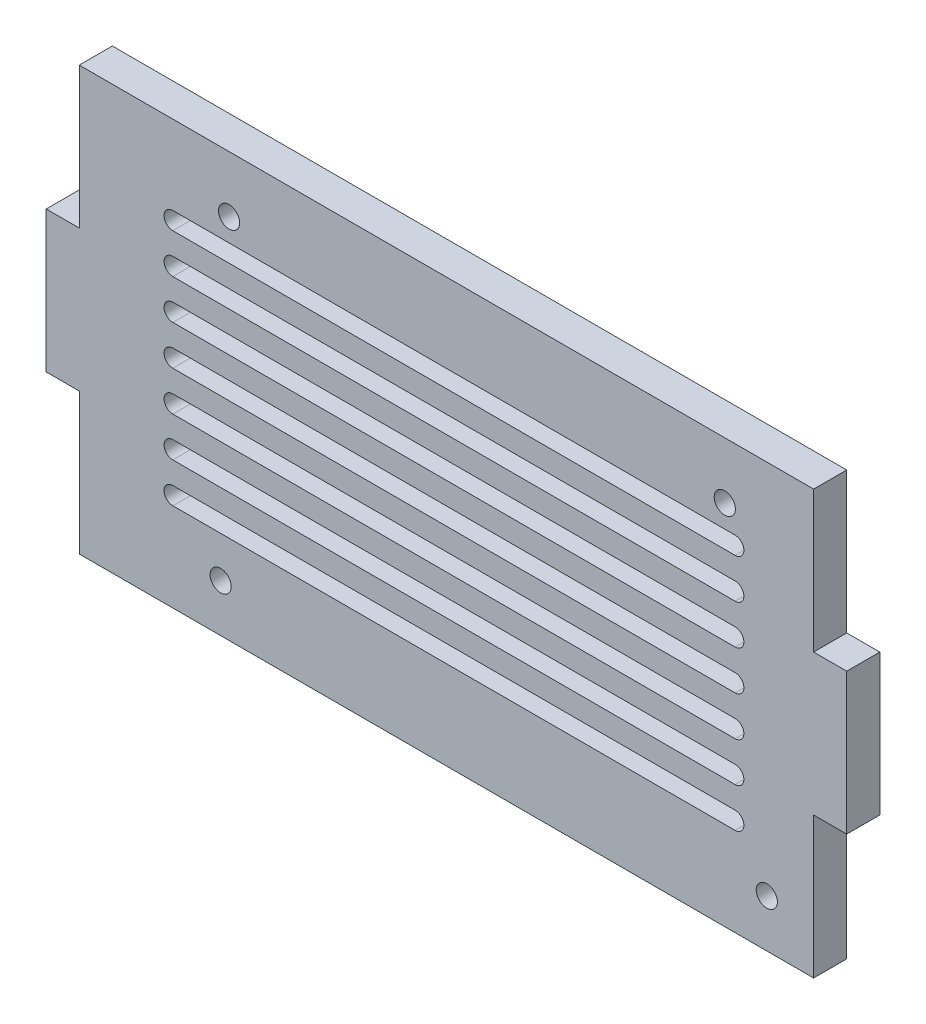
SolidWorks part; units mm, degrees
ref_plane "Alzado" through (0, 0, 0) normal (0, 0, 1) x (1, 0, 0)
ref_plane "Planta" through (0, 0, 0) normal (0, 1, 0) x (1, 0, 0)
ref_plane "Vista lateral" through (0, 0, 0) normal (1, 0, 0) x (0, 0, -1)
sketch "Croquis1" plane through (0, 0, 0) normal (0, 0, 1) x (1, 0, 0)
  line L0 (63.2484, 20.3599) -> (-33.2876, 20.3599)
  line L1 (-34.2876, 19.3599) -> (-34.2876, -31.9801)
  line L2 (-33.2876, -32.9801) -> (63.7724, -32.9801)
  line L3 (64.7724, -31.9801) -> (64.7724, -30.4401)
  line L4 (64.7724, -30.4401) -> (67.3124, -27.9001)
  line L5 (67.3124, -27.9001) -> (67.3124, 4.8659)
  line L6 (67.3124, 4.8659) -> (64.7724, 7.4059)
  line L7 (64.7724, 7.4059) -> (64.7724, 18.8359)
  line L8 (64.7724, 18.8359) -> (63.2484, 20.3599)
  line L9 (-27.5479, 13.0737) -> (57.4412, 13.0737) construction
  line L10 (-41.6876, 26.3599) -> (69.3124, 26.3599)
  line L11 (-41.6876, 26.3599) -> (-41.6876, -37.6401)
  line L12 (-41.6876, -37.6401) -> (69.3124, -37.6401)
  line L13 (69.3124, 26.3599) -> (69.3124, -37.6401)
  line L14 (-27.5479, 14.3982) -> (57.4412, 14.3982)
  line L15 (-27.5479, 11.7492) -> (57.4412, 11.7492)
  line L16 (-27.5479, 7.0737) -> (57.4412, 7.0737) construction
  line L17 (-27.5479, 8.3982) -> (57.4412, 8.3982)
  line L18 (-27.5479, 5.7492) -> (57.4412, 5.7492)
  line L19 (-27.5479, 1.0737) -> (57.4412, 1.0737) construction
  line L20 (-27.5479, 2.3982) -> (57.4412, 2.3982)
  line L21 (-27.5479, -0.2508) -> (57.4412, -0.2508)
  line L22 (-27.5479, -4.9263) -> (57.4412, -4.9263) construction
  line L23 (-27.5479, -3.6018) -> (57.4412, -3.6018)
  line L24 (-27.5479, -6.2508) -> (57.4412, -6.2508)
  line L25 (-27.5479, -10.9263) -> (57.4412, -10.9263) construction
  line L26 (-27.5479, -9.6018) -> (57.4412, -9.6018)
  line L27 (-27.5479, -12.2508) -> (57.4412, -12.2508)
  line L28 (-27.5479, -16.9263) -> (57.4412, -16.9263) construction
  line L29 (-27.5479, -15.6018) -> (57.4412, -15.6018)
  line L30 (-27.5479, -18.2508) -> (57.4412, -18.2508)
  line L31 (-27.5479, -22.9263) -> (57.4412, -22.9263) construction
  line L32 (-27.5479, -21.6018) -> (57.4412, -21.6018)
  line L33 (-27.5479, -24.2508) -> (57.4412, -24.2508)
  circle A4 centre (-20.3176, -30.4401) radius 1.6
  circle A5 centre (-19.0476, 17.8199) radius 1.6
  circle A6 centre (55.8824, 17.8199) radius 1.6
  circle A7 centre (62.2324, -30.4401) radius 1.6
  arc A8 (-33.2876, 20.3599) -> (-34.2876, 19.3599) centre (-33.2876, 19.3599) ccw
  arc A9 (-34.2876, -31.9801) -> (-33.2876, -32.9801) centre (-33.2876, -31.9801) ccw
  arc A10 (63.7724, -32.9801) -> (64.7724, -31.9801) centre (63.7724, -31.9801) ccw
  arc A39 (-27.5479, 14.3982) -> (-27.5479, 11.7492) centre (-27.5479, 13.0737) ccw
  arc A40 (57.4412, 11.7492) -> (57.4412, 14.3982) centre (57.4412, 13.0737) ccw
  arc A41 (-27.5479, 8.3982) -> (-27.5479, 5.7492) centre (-27.5479, 7.0737) ccw
  arc A42 (57.4412, 5.7492) -> (57.4412, 8.3982) centre (57.4412, 7.0737) ccw
  arc A43 (-27.5479, 2.3982) -> (-27.5479, -0.2508) centre (-27.5479, 1.0737) ccw
  arc A44 (57.4412, -0.2508) -> (57.4412, 2.3982) centre (57.4412, 1.0737) ccw
  arc A45 (-27.5479, -3.6018) -> (-27.5479, -6.2508) centre (-27.5479, -4.9263) ccw
  arc A46 (57.4412, -6.2508) -> (57.4412, -3.6018) centre (57.4412, -4.9263) ccw
  arc A47 (-27.5479, -9.6018) -> (-27.5479, -12.2508) centre (-27.5479, -10.9263) ccw
  arc A48 (57.4412, -12.2508) -> (57.4412, -9.6018) centre (57.4412, -10.9263) ccw
  arc A49 (-27.5479, -15.6018) -> (-27.5479, -18.2508) centre (-27.5479, -16.9263) ccw
  arc A50 (57.4412, -18.2508) -> (57.4412, -15.6018) centre (57.4412, -16.9263) ccw
  arc A51 (-27.5479, -21.6018) -> (-27.5479, -24.2508) centre (-27.5479, -22.9263) ccw
  arc A52 (57.4412, -24.2508) -> (57.4412, -21.6018) centre (57.4412, -22.9263) ccw
  point P30 (14.9467, 13.0737)
  point P38 (14.9467, 7.0737)
  point P45 (14.9467, 1.0737)
  point P52 (14.9467, -4.9263)
  point P59 (14.9467, -10.9263)
  point P66 (14.9467, -16.9263)
  point P73 (14.9467, -22.9263)
  dimension "D1" = 3.2
  dimension "D2" = 1
  dimension "D3" = 55.8824
  dimension "D4" = 62.2324
  dimension "D5" = 63.2484
  dimension "D6" = 64.7724
  dimension "D7" = 67.3124
  dimension "D8" = 19.0476
  dimension "D9" = 20.3176
  dimension "D10" = 34.2876
  dimension "D11" = 4.8659
  dimension "D12" = 7.4059
  dimension "D13" = 17.8199
  dimension "D14" = 18.8359
  dimension "D15" = 20.3599
  dimension "D16" = 27.9001
  dimension "D17" = 111
  dimension "D18" = 32.9801
  dimension "D19" = 64
  dimension "D20" = 6
  dimension "D21" = 7
  dimension "D23" = 2
extrude "Saliente-Extruir1" add sketch "Croquis1" along normal blind 5 contours L13 L10 L11 L12 A10 L2 A9 L1 A8 L0 L8 L7 L6 L5 L4 L3 | L2 A10 L3 L4 L5 L6 L7 L8 L0 A8 L1 A9 A4 A5 A6 A7
sketch "Croquis2" plane through (-41.6876, 0, 0) normal (-1, 0, 0) x (0, 0, 1)
  line L0 (0, 26.3599) -> (0, -37.6401) construction
  line L1 (0, 5.0266) -> (5, 5.0266)
  line L2 (0, 5.0266) -> (0, -16.3067)
  line L3 (0, -16.3067) -> (5, -16.3067)
  line L4 (5, 5.0266) -> (5, -16.3067)
  line L5 (5, 26.3599) -> (5, -37.6401) construction
  line L6 (5, 26.3599) -> (0, 26.3599) construction
  dimension "D1" = 21.3333
  dimension "D2" = 21.3333
extrude "Saliente-Extruir2" add sketch "Croquis2" along normal blind 5
sketch "Croquis3" plane through (69.3124, 0, 0) normal (1, 0, 0) x (0, 0, -1)
  line L0 (-5, 26.3599) -> (-5, -37.6401) construction
  line L1 (-5, 5.0266) -> (0, 5.0266)
  line L2 (-5, 5.0266) -> (-5, -16.3067)
  line L3 (-5, -16.3067) -> (0, -16.3067)
  line L4 (0, 5.0266) -> (0, -16.3067)
  line L5 (0, 26.3599) -> (0, -37.6401) construction
  line L6 (-5, 26.3599) -> (0, 26.3599) construction
  dimension "D1" = 21.3333
  dimension "D2" = 21.3333
extrude "Saliente-Extruir3" add sketch "Croquis3" along normal blind 5
sketch "Croquis4" plane through (0, 0, 5) normal (0, 0, 1) x (1, 0, 0)
  line L0 (-27.5479, -0.2508) -> (57.4412, -0.2508) construction
  line L1 (-27.5479, 14.3982) -> (57.4412, 14.3982) construction
  line L2 (-27.5479, 11.7492) -> (57.4412, 11.7492) construction
  line L3 (-27.5479, 8.3982) -> (57.4412, 8.3982) construction
  line L4 (-27.5479, 5.7492) -> (57.4412, 5.7492) construction
  line L5 (-27.5479, 2.3982) -> (57.4412, 2.3982) construction
  line L6 (-27.5479, -3.6018) -> (57.4412, -3.6018) construction
  line L7 (-27.5479, -6.2508) -> (57.4412, -6.2508) construction
  line L8 (-27.5479, -9.6018) -> (57.4412, -9.6018) construction
  line L9 (-27.5479, -12.2508) -> (57.4412, -12.2508) construction
  line L10 (-27.5479, -18.2508) -> (57.4412, -18.2508) construction
  line L11 (-27.5479, -15.6018) -> (57.4412, -15.6018) construction
  line L12 (69.3124, 5.0266) -> (69.3124, 26.3599)
  line L13 (69.3124, 26.3599) -> (-41.6876, 26.3599)
  line L14 (-41.6876, 26.3599) -> (-41.6876, 5.0266)
  line L15 (-41.6876, 5.0266) -> (-46.6876, 5.0266)
  line L16 (-46.6876, 5.0266) -> (-46.6876, -16.3067)
  line L17 (-46.6876, -16.3067) -> (-41.6876, -16.3067)
  line L18 (-41.6876, -16.3067) -> (-41.6876, -37.6401)
  line L19 (-41.6876, -37.6401) -> (69.3124, -37.6401)
  line L20 (69.3124, -37.6401) -> (69.3124, -16.3067)
  line L21 (69.3124, -16.3067) -> (74.3124, -16.3067)
  line L22 (74.3124, -16.3067) -> (74.3124, 5.0266)
  line L23 (74.3124, 5.0266) -> (69.3124, 5.0266)
  line L24 (69.3124, 5.0266) -> (69.3124, 26.3599)
  line L25 (69.3124, 26.3599) -> (-41.6876, 26.3599)
  line L26 (-41.6876, 26.3599) -> (-41.6876, 5.0266)
  line L27 (-41.6876, 5.0266) -> (-46.6876, 5.0266)
  line L28 (-46.6876, 5.0266) -> (-46.6876, -16.3067)
  line L29 (-46.6876, -16.3067) -> (-41.6876, -16.3067)
  line L30 (-41.6876, -16.3067) -> (-41.6876, -37.6401)
  line L31 (-41.6876, -37.6401) -> (69.3124, -37.6401)
  line L32 (69.3124, -37.6401) -> (69.3124, -16.3067)
  line L33 (69.3124, -16.3067) -> (74.3124, -16.3067)
  line L34 (74.3124, -16.3067) -> (74.3124, 5.0266)
  line L35 (74.3124, 5.0266) -> (69.3124, 5.0266)
  line L36 (-27.5479, -21.6018) -> (57.4412, -21.6018) construction
  line L37 (-27.5479, -24.2508) -> (57.4412, -24.2508) construction
  line L38 (-27.5479, -0.2508) -> (57.4412, -0.2508)
  line L39 (-27.5479, 14.3982) -> (57.4412, 14.3982)
  line L40 (-27.5479, 11.7492) -> (57.4412, 11.7492)
  line L41 (-27.5479, 8.3982) -> (57.4412, 8.3982)
  line L42 (-27.5479, 5.7492) -> (57.4412, 5.7492)
  line L43 (-27.5479, 2.3982) -> (57.4412, 2.3982)
  line L44 (-27.5479, -3.6018) -> (57.4412, -3.6018)
  line L45 (-27.5479, -6.2508) -> (57.4412, -6.2508)
  line L46 (-27.5479, -9.6018) -> (57.4412, -9.6018)
  line L47 (-27.5479, -12.2508) -> (57.4412, -12.2508)
  line L48 (-27.5479, -18.2508) -> (57.4412, -18.2508)
  line L49 (-27.5479, -15.6018) -> (57.4412, -15.6018)
  line L50 (-27.5479, -21.6018) -> (57.4412, -21.6018)
  line L51 (-27.5479, -24.2508) -> (57.4412, -24.2508)
  arc A0 (57.4412, -24.2508) -> (57.4412, -21.6018) centre (57.4412, -22.9263) ccw construction
  arc A1 (57.4412, -18.2508) -> (57.4412, -15.6018) centre (57.4412, -16.9263) ccw construction
  arc A2 (57.4412, -12.2508) -> (57.4412, -9.6018) centre (57.4412, -10.9263) ccw construction
  arc A3 (57.4412, -6.2508) -> (57.4412, -3.6018) centre (57.4412, -4.9263) ccw construction
  arc A4 (57.4412, -0.2508) -> (57.4412, 2.3982) centre (57.4412, 1.0737) ccw construction
  arc A5 (57.4412, 5.7492) -> (57.4412, 8.3982) centre (57.4412, 7.0737) ccw construction
  arc A6 (57.4412, 11.7492) -> (57.4412, 14.3982) centre (57.4412, 13.0737) ccw construction
  arc A7 (-27.5479, -21.6018) -> (-27.5479, -24.2508) centre (-27.5479, -22.9263) ccw construction
  arc A8 (-27.5479, -15.6018) -> (-27.5479, -18.2508) centre (-27.5479, -16.9263) ccw construction
  arc A9 (-27.5479, -9.6018) -> (-27.5479, -12.2508) centre (-27.5479, -10.9263) ccw construction
  arc A10 (-27.5479, -3.6018) -> (-27.5479, -6.2508) centre (-27.5479, -4.9263) ccw construction
  arc A11 (-27.5479, 2.3982) -> (-27.5479, -0.2508) centre (-27.5479, 1.0737) ccw construction
  arc A12 (-27.5479, 8.3982) -> (-27.5479, 5.7492) centre (-27.5479, 7.0737) ccw construction
  arc A13 (-27.5479, 14.3982) -> (-27.5479, 11.7492) centre (-27.5479, 13.0737) ccw construction
  circle A14 centre (-20.3176, -30.4401) radius 1.6 construction
  circle A15 centre (62.2324, -30.4401) radius 1.6 construction
  circle A16 centre (55.8824, 17.8199) radius 1.6 construction
  circle A17 centre (-19.0476, 17.8199) radius 1.6 construction
  arc A18 (57.4412, -24.2508) -> (57.4412, -21.6018) centre (57.4412, -22.9263) ccw
  arc A19 (57.4412, -18.2508) -> (57.4412, -15.6018) centre (57.4412, -16.9263) ccw
  arc A20 (57.4412, -12.2508) -> (57.4412, -9.6018) centre (57.4412, -10.9263) ccw
  arc A21 (57.4412, -6.2508) -> (57.4412, -3.6018) centre (57.4412, -4.9263) ccw
  arc A22 (57.4412, -0.2508) -> (57.4412, 2.3982) centre (57.4412, 1.0737) ccw
  arc A23 (57.4412, 5.7492) -> (57.4412, 8.3982) centre (57.4412, 7.0737) ccw
  arc A24 (57.4412, 11.7492) -> (57.4412, 14.3982) centre (57.4412, 13.0737) ccw
  arc A25 (-27.5479, -21.6018) -> (-27.5479, -24.2508) centre (-27.5479, -22.9263) ccw
  arc A26 (-27.5479, -15.6018) -> (-27.5479, -18.2508) centre (-27.5479, -16.9263) ccw
  arc A27 (-27.5479, -9.6018) -> (-27.5479, -12.2508) centre (-27.5479, -10.9263) ccw
  arc A28 (-27.5479, -3.6018) -> (-27.5479, -6.2508) centre (-27.5479, -4.9263) ccw
  arc A29 (-27.5479, 2.3982) -> (-27.5479, -0.2508) centre (-27.5479, 1.0737) ccw
  arc A30 (-27.5479, 8.3982) -> (-27.5479, 5.7492) centre (-27.5479, 7.0737) ccw
  arc A31 (-27.5479, 14.3982) -> (-27.5479, 11.7492) centre (-27.5479, 13.0737) ccw
  circle A32 centre (-20.3176, -30.4401) radius 1.6
  circle A33 centre (62.2324, -30.4401) radius 1.6
  circle A34 centre (55.8824, 17.8199) radius 1.6
  circle A35 centre (-19.0476, 17.8199) radius 1.6
  dimension "D1" = 0
